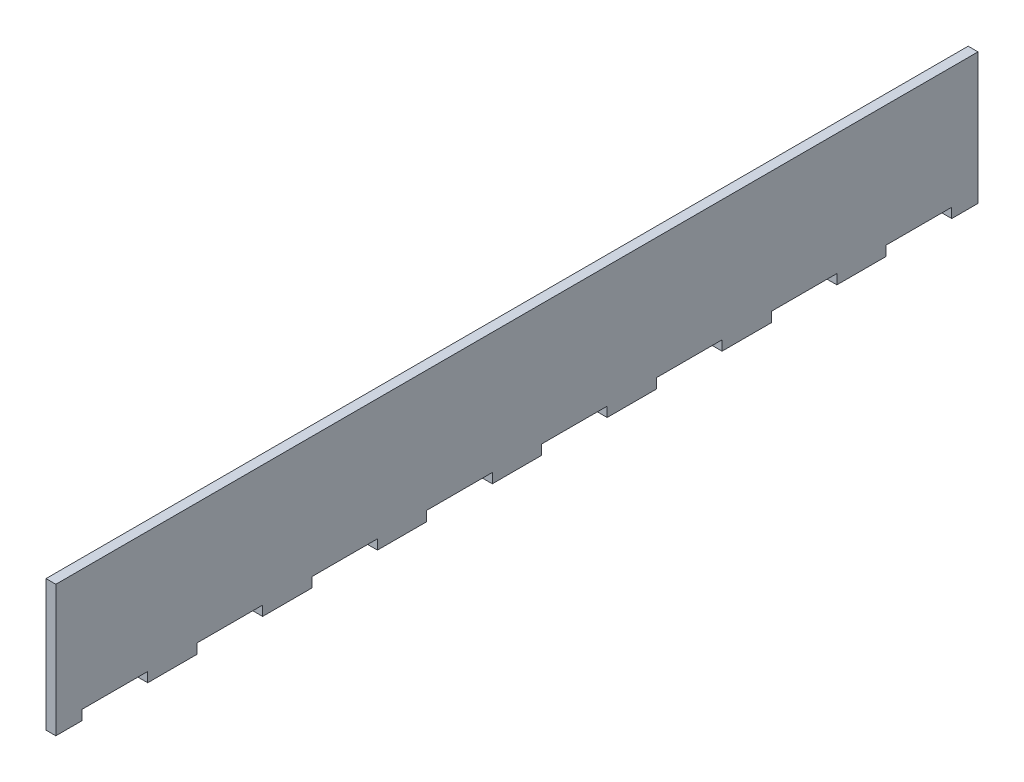
SolidWorks part; units mm, degrees
ref_plane "Front Plane" through (0, 0, 0) normal (0, 0, 1) x (1, 0, 0)
ref_plane "Top Plane" through (0, 0, 0) normal (0, 1, 0) x (1, 0, 0)
ref_plane "Right Plane" through (0, 0, 0) normal (1, 0, 0) x (0, 0, -1)
sketch "Sketch1" plane through (0, 0, 0) normal (1, 0, 0) x (0, 0, -1)
  line L0 (28, 0) -> (43, 0)
  line L1 (0, 0) -> (8, 0)
  line L2 (0, 0) -> (0, 40)
  line L3 (0, 40) -> (281, 40)
  line L4 (281, 0) -> (281, 40)
  line L7 (43, 0) -> (43, 3)
  line L8 (8, 0) -> (8, 3)
  line L9 (8, 3) -> (28, 3)
  line L10 (28, 0) -> (28, 3)
  line L13 (43, 3) -> (63, 3)
  line L14 (63, 0) -> (63, 3)
  line L15 (78, 0) -> (78, 3)
  line L16 (78, 3) -> (98, 3)
  line L17 (98, 0) -> (98, 3)
  line L18 (113, 0) -> (113, 3)
  line L19 (113, 3) -> (133, 3)
  line L20 (133, 0) -> (133, 3)
  line L21 (148, 0) -> (148, 3)
  line L22 (148, 3) -> (168, 3)
  line L23 (168, 0) -> (168, 3)
  line L24 (183, 0) -> (183, 3)
  line L25 (183, 3) -> (203, 3)
  line L26 (203, 0) -> (203, 3)
  line L27 (218, 0) -> (218, 3)
  line L28 (218, 3) -> (238, 3)
  line L29 (238, 0) -> (238, 3)
  line L30 (253, 0) -> (253, 3)
  line L31 (253, 3) -> (273, 3)
  line L32 (273, 0) -> (273, 3)
  line L33 (63, 0) -> (78, 0)
  line L34 (98, 0) -> (113, 0)
  line L35 (133, 0) -> (148, 0)
  line L36 (168, 0) -> (183, 0)
  line L37 (203, 0) -> (218, 0)
  line L38 (238, 0) -> (253, 0)
  line L39 (273, 0) -> (281, 0)
  point P10 (0, 0)
  point P12 (0, 0)
  dimension "D1" = 20
  dimension "D2" = 8
  dimension "D3" = 281
  dimension "D4" = 3
  dimension "D6" = 40
  dimension "D7" = 15
  dimension "D5" = 8
extrude "Boss-Extrude1" add sketch "Sketch1" along normal blind 3 contours L3 L4 L39 L32 L31 L30 L38 L29 L28 L27 L37 L26 L25 L24 L36 L23 L22 L21 L35 L20 L19 L18 L34 L17 L16 L15 L33 L14 L13 L7 L0 L10 L9 L8 L1 L2
